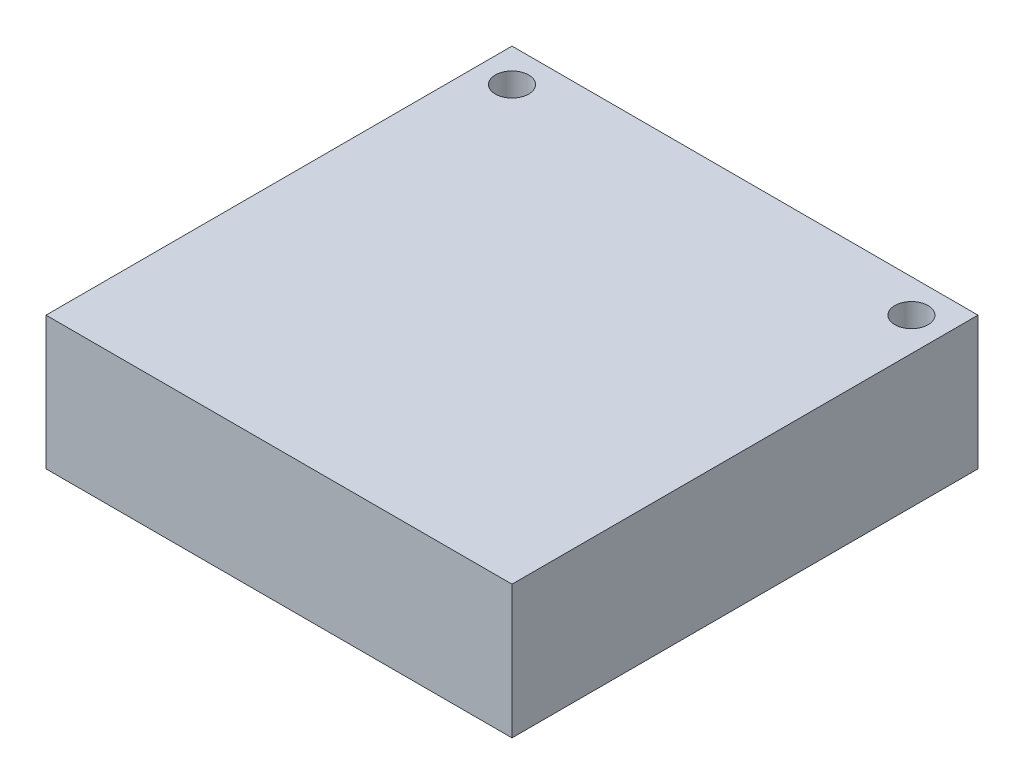
SolidWorks part; units mm, degrees
ref_plane "Front Plane" through (0, 0, 0) normal (0, 0, 1) x (1, 0, 0)
ref_plane "Top Plane" through (0, 0, 0) normal (0, 1, 0) x (1, 0, 0)
ref_plane "Right Plane" through (0, 0, 0) normal (1, 0, 0) x (0, 0, -1)
sketch "Sketch1" plane through (0, 0, 0) normal (0, 1, 0) x (1, 0, 0)
  line L1 (0, 0) -> (-28, 0)
  line L2 (0, 0) -> (0, -28)
  line L3 (0, -28) -> (-28, -28)
  line L4 (-28, 0) -> (-28, -28)
  dimension "D1" = 28
  dimension "D2" = 28
extrude "Boss-Extrude1" add sketch "Sketch1" along normal blind 8
sketch "Sketch2" plane through (0, 8, 0) normal (0, 1, 0) x (1, 0, 0)
  line L0 (-28, 0) -> (-28, -28) construction
  line L1 (0, 0) -> (-28, 0) construction
  line L2 (0, -28) -> (0, 0) construction
  circle A0 centre (-26, -2) radius 1
  circle A1 centre (-2, -2) radius 1
  point P10 (0, 0)
  point P12 (-1.8218, -3.3912)
  dimension "D3" = 2
  dimension "D4" = 2
  dimension "D1" = 2
  dimension "D2" = 2
  dimension "D5" = 2
  dimension "D6" = 2
extrude "Cut-Extrude1" cut sketch "Sketch2" against normal blind 8
